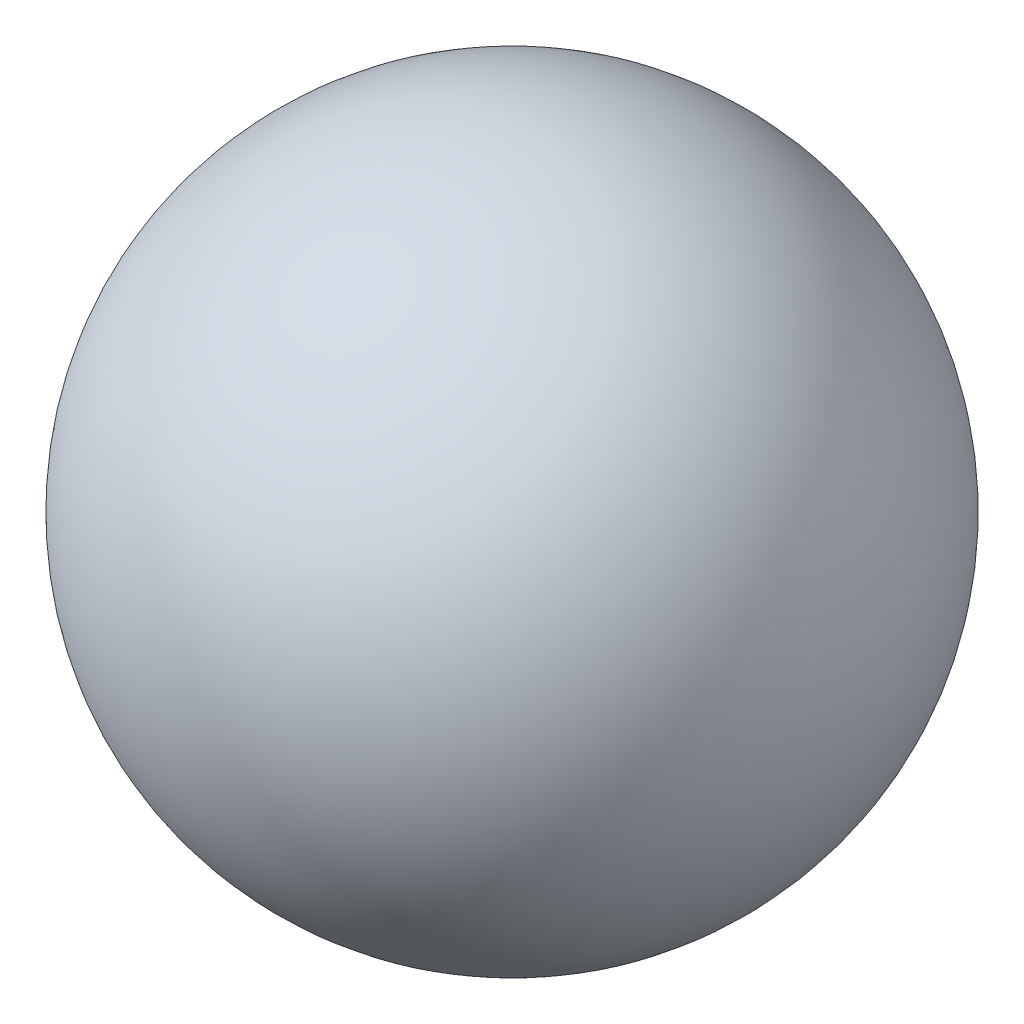
SolidWorks part; units mm, degrees
ref_plane "Alzado" through (0, 0, 0) normal (0, 0, 1) x (1, 0, 0)
ref_plane "Planta" through (0, 0, 0) normal (0, 1, 0) x (1, 0, 0)
ref_plane "Vista lateral" through (0, 0, 0) normal (1, 0, 0) x (0, 0, -1)
sketch "Croquis1" plane through (0, 0, 0) normal (0, 0, 1) x (1, 0, 0)
  line L0 (-52.0193, 52.7444) -> (-52.0193, 39.2444)
  arc A0 (-52.0193, 39.2444) -> (-52.0193, 52.7444) centre (-52.0193, 45.9944) ccw
  dimension "D1" = 13.5
revolve "Revolución1" add sketch "Croquis1" angle 360 about L0
